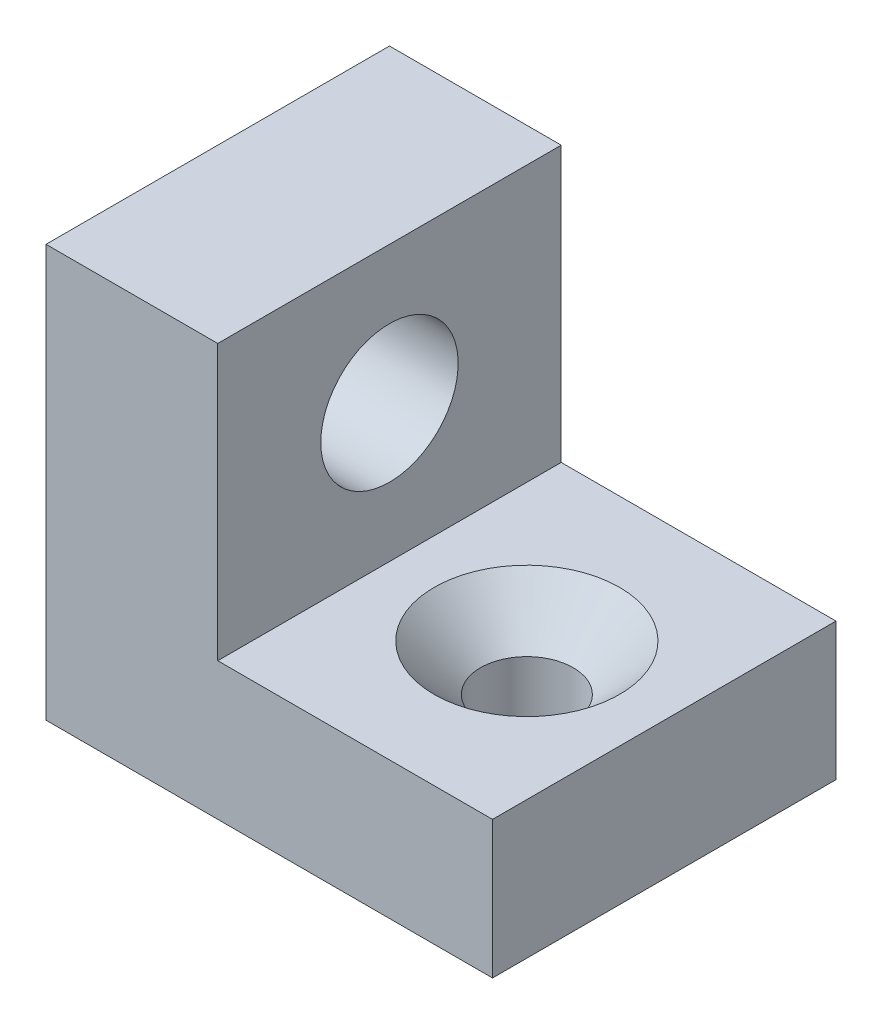
SolidWorks part; units mm, degrees
ref_plane "Front Plane" through (0, 0, 0) normal (0, 0, 1) x (1, 0, 0)
ref_plane "Top Plane" through (0, 0, 0) normal (0, 1, 0) x (1, 0, 0)
ref_plane "Right Plane" through (0, 0, 0) normal (1, 0, 0) x (0, 0, -1)
sketch "Sketch1" plane through (0, 0, 0) normal (0, 1, 0) x (1, 0, 0)
  line L1 (0, 0) -> (40, 0)
  line L2 (0, 0) -> (0, -50)
  line L3 (0, -50) -> (40, -50)
  line L4 (40, 0) -> (40, -50)
  dimension "D1" = 50
  dimension "D2" = 40
extrude "Boss-Extrude1" add sketch "Sketch1" along normal blind 20
hole_wizard "CSK for M2 Flat Head Machine Screw1" positions "Sketch2" profile "Sketch3" countersink size "M2" standard "ANSI Metric" end condition through all
sketch "Sketch2" plane through (0, 20, 0) normal (0, 1, 0) x (1, 0, 0)
  line L0 (0, -50) -> (40, -50) construction
  line L1 (0, 0) -> (0, -50) construction
  point P0 (20, -25)
  dimension "D1" = 25
  dimension "D2" = 20
sketch "Sketch3" plane through (20, 20, 25) normal (1, 0, 0) x (0, 0, 1)
  line L0 (0, 0) -> (0, 20)
  line L1 (0, 20) -> (6.75, 20)
  line L2 (6.75, 20) -> (6.75, 6.75)
  line L3 (6.75, 6.75) -> (13.5, 0)
  line L5 (13.5, 0) -> (0, 0)
  line L6 (-6.75, 6.75) -> (-13.5, 0) construction
  line L11 (0, -6.35) -> (0, 107.95) construction
  dimension "Thru Hole Dia." = 13.5
  dimension "Thru Hole Depth" = 20
  dimension "Near C'Sink Dia." = 27
  dimension "Near C'Sink Angle" = 90
sketch "Sketch4" plane through (0, 0, 0) normal (-1, 0, 0) x (0, 0, 1)
  line L1 (0, 0) -> (50, 0)
  line L2 (0, 0) -> (0, 60)
  line L3 (0, 60) -> (50, 60)
  line L4 (50, 0) -> (50, 60)
  circle A0 centre (25, 40) radius 10
  dimension "D3" = 20
  dimension "D1" = 60
  dimension "D2" = 50
  dimension "D4" = 20
  dimension "D5" = 25
extrude "Boss-Extrude2" add sketch "Sketch4" along normal blind 25
